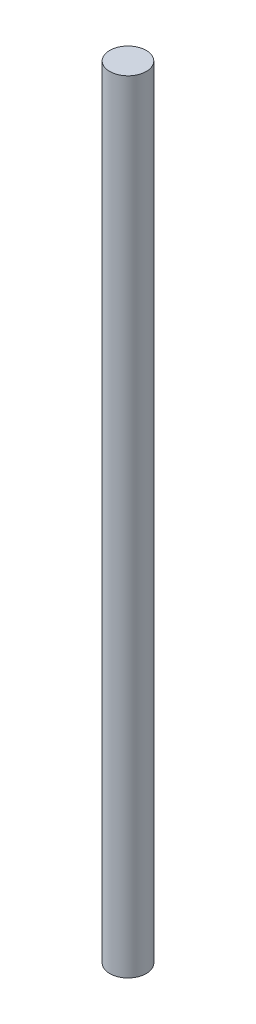
SolidWorks part; units mm, degrees
ref_plane "Front Plane" through (0, 0, 0) normal (0, 0, 1) x (1, 0, 0)
ref_plane "Top Plane" through (0, 0, 0) normal (0, 1, 0) x (1, 0, 0)
ref_plane "Right Plane" through (0, 0, 0) normal (1, 0, 0) x (0, 0, -1)
sketch "Sketch1" plane through (0, 0, 0) normal (0, 1, 0) x (1, 0, 0)
  circle A0 centre (0, 0) radius 914.4
  dimension "D1" = 1828.8
extrude "Boss-Extrude1" add sketch "Sketch1" along normal blind 39116
